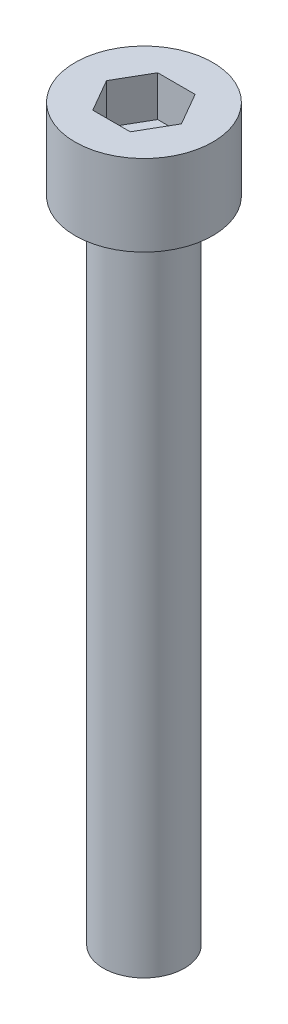
SolidWorks part; units mm, degrees
material "AISI 304"
ref_plane "前视基准面" through (0, 0, 0) normal (0, 0, 1) x (1, 0, 0)
ref_plane "上视基准面" through (0, 0, 0) normal (0, 1, 0) x (1, 0, 0)
ref_plane "右视基准面" through (0, 0, 0) normal (1, 0, 0) x (0, 0, -1)
sketch "草图1" plane through (0, 0, 0) normal (0, 1, 0) x (1, 0, 0)
  circle A0 centre (0, 0) radius 4.25
  dimension "D1" = 8.5
extrude "凸台-拉伸1" add sketch "草图1" along normal blind 5
sketch "草图2" plane through (0, 5, 0) normal (0, 1, 0) x (1, 0, 0)
  line L1 (2.3094, 0) -> (1.1547, 2)
  line L2 (1.1547, 2) -> (-1.1547, 2)
  line L3 (-1.1547, 2) -> (-2.3094, 0)
  line L4 (-2.3094, 0) -> (-1.1547, -2)
  line L5 (-1.1547, -2) -> (1.1547, -2)
  line L6 (1.1547, -2) -> (2.3094, 0)
  circle A0 centre (0, 0) radius 2 construction
  dimension "D1" = 4
extrude "切除-拉伸1" cut sketch "草图2" against normal blind 2.5
sketch "草图3" plane through (0, 0, 0) normal (0, -1, 0) x (1, 0, 0)
  circle A0 centre (0, 0) radius 2.5
  dimension "D1" = 5
extrude "凸台-拉伸2" add sketch "草图3" along normal blind 40
